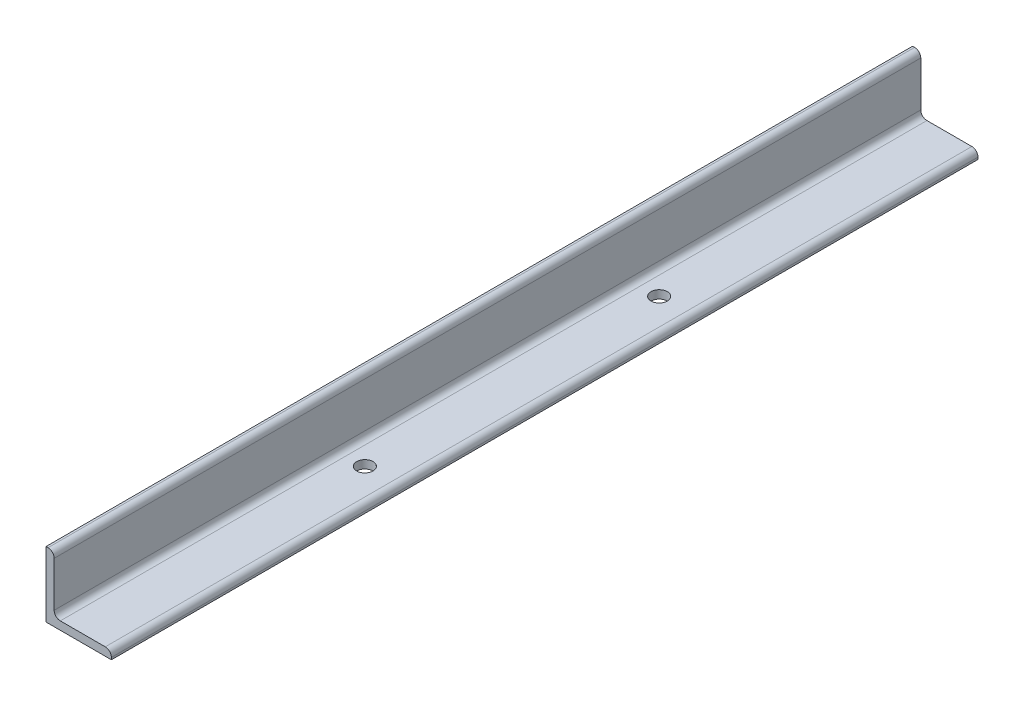
SolidWorks part; units mm, degrees
ref_plane "Front Plane" through (0, 0, 0) normal (0, 0, 1) x (1, 0, 0)
ref_plane "Top Plane" through (0, 0, 0) normal (0, 1, 0) x (1, 0, 0)
ref_plane "Right Plane" through (0, 0, 0) normal (1, 0, 0) x (0, 0, -1)
sketch "Sketch1" plane through (0, 0, 0) normal (0, 0, 1) x (1, 0, 0)
  line L0 (0, 0) -> (0, 50.8)
  line L1 (0, 50.8) -> (1.5926, 50.8)
  line L2 (6.35, 46.0426) -> (6.35, 11.1125)
  line L3 (11.1125, 6.35) -> (46.0426, 6.35)
  line L4 (50.8, 1.5926) -> (50.8, 0)
  line L5 (50.8, 0) -> (0, 0)
  arc A0 (50.8, 1.5926) -> (46.0426, 6.35) centre (46.0426, 1.5926) ccw
  arc A1 (1.5926, 50.8) -> (6.35, 46.0426) centre (1.5926, 46.0426) cw
  arc A2 (11.1125, 6.35) -> (6.35, 11.1125) centre (11.1125, 11.1125) cw
  circle A3 centre (0, 0) radius 4.7625 construction
  dimension "D2" = 1.5926
  dimension "Radius_1" = 4.7625
  dimension "Radius_2" = 4.7625
  dimension "D1" = 6.35
  dimension "V_leg" = 50.8
  dimension "H_leg" = 50.8
  dimension "Thickness" = 6.35
  dimension "Flat_wid" = 1.5926
extrude "Boss-Extrude1" add sketch "Sketch1" along normal mid plane 673.1
sketch "Sketch2" plane through (0, 0, 0) normal (0, -1, 0) x (1, 0, 0)
  line L0 (25.4, -336.55) -> (25.4, 336.55) construction
  line L1 (0, -336.55) -> (50.8, -336.55) construction
  line L2 (0, 336.55) -> (50.8, 336.55) construction
  circle A0 centre (25.4, -114.3) radius 6.35
  circle A1 centre (25.4, 114.3) radius 6.35
  dimension "D1" = 222.25
  dimension "D2" = 450.85
extrude "Cut-Extrude1" cut sketch "Sketch2" against normal through all
